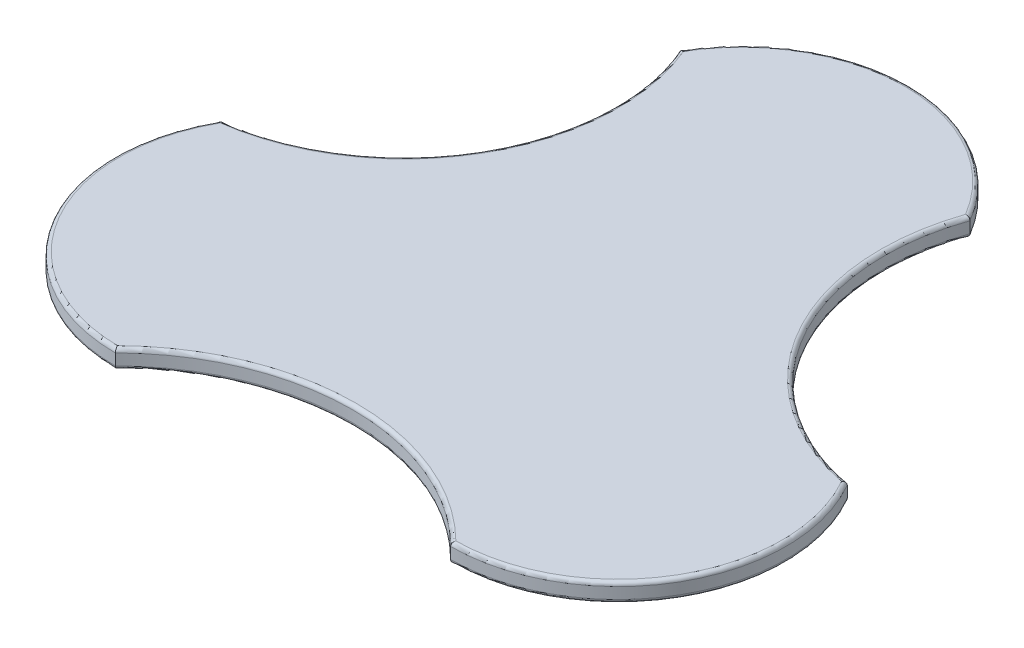
SolidWorks part; units mm, degrees
ref_plane "Front Plane" through (0, 0, 0) normal (0, 0, 1) x (1, 0, 0)
ref_plane "Top Plane" through (0, 0, 0) normal (0, 1, 0) x (1, 0, 0)
ref_plane "Right Plane" through (0, 0, 0) normal (1, 0, 0) x (0, 0, -1)
sketch "Sketch1" plane through (0, 0, 0) normal (0, 1, 0) x (1, 0, 0)
  line L3 (0, 0) -> (9, 15.5885) construction
  line L4 (9, 15.5885) -> (18, 0) construction
  line L5 (18, 0) -> (0, 0) construction
  arc A0 (-7.7942, 4.5) -> (1.2058, 20.0885) centre (-9.1547, 15.6778) ccw
  arc A1 (18, -9) -> (25.7942, 4.5) centre (18, 0) ccw
  arc A2 (0, -9) -> (18, -9) centre (9, -18) cw
  arc A3 (-7.7942, 4.5) -> (0, -9) centre (0, 0) ccw
  arc A4 (16.7942, 20.0885) -> (1.2058, 20.0885) centre (9, 15.5885) ccw
  arc A5 (25.7942, 4.5) -> (16.7942, 20.0885) centre (27.9886, 16.1592) cw
  point P14 (0, 0)
  dimension "D1" = 9
  dimension "D2" = 18
extrude "Boss-Extrude1" add sketch "Sketch1" along normal mid plane 1
fillet "Fillet1" radius 0.2 12 edges at (9, -0.5, -24.5885) (-7.7942, -0.5, 4.5) (25.7942, -0.5, 4.5) (-7.7942, 0.5, 4.5) (9, 0.5, -24.5885) (25.7942, 0.5, 4.5) (0.597, -0.5, -10.0477) (9, -0.5, 5.2721) (17.7141, -0.5, -10.2273) (9, 0.5, 5.2721) (0.597, 0.5, -10.0477) (17.7141, 0.5, -10.2273)
